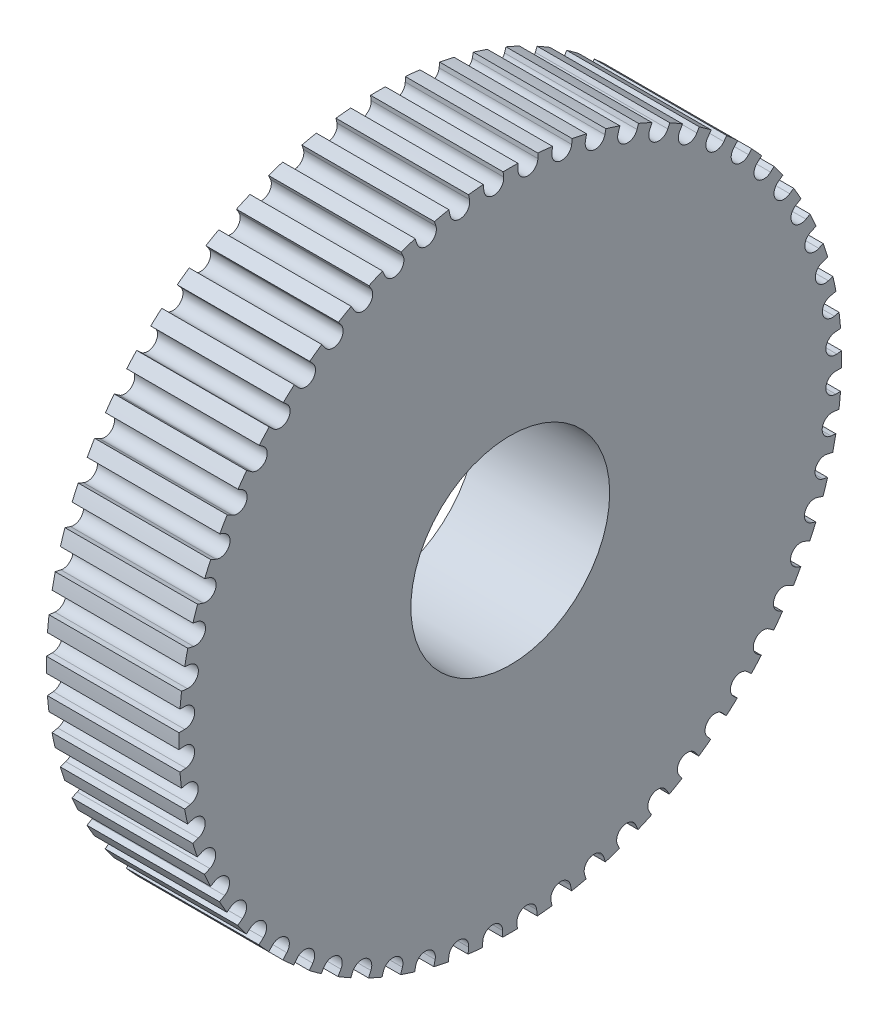
SolidWorks part; units mm, degrees
material "PA Type 6"
ref_plane "Front Plane" through (0, 0, 0) normal (0, 0, 1) x (1, 0, 0)
ref_plane "Top Plane" through (0, 0, 0) normal (0, 1, 0) x (1, 0, 0)
ref_plane "Right Plane" through (0, 0, 0) normal (1, 0, 0) x (0, 0, -1)
sketch "Sketch1" plane through (0, 0, 0) normal (1, 0, 0) x (0, 0, -1)
  circle A0 centre (0, 0) radius 6
  circle A1 centre (0, 0) radius 20
extrude "Boss-Extrude1" add sketch "Sketch1" along normal blind 8
sketch "Sketch2" plane through (8, 0, 0) normal (1, 0, 0) x (0, 0, -1)
  line L0 (1.0615, 20.6675) -> (1.0615, 19.6426) construction
  line L1 (1.6615, 20.6675) -> (1.6615, 19.6426)
  line L2 (0.4615, 20.6675) -> (0.4615, 19.6426)
  arc A0 (1.6615, 20.6675) -> (0.4615, 20.6675) centre (1.0615, 20.6675) ccw
  arc A1 (0.4615, 19.6426) -> (1.6615, 19.6426) centre (1.0615, 19.6426) ccw
  point P2 (1.0615, 20.155)
  point P7 (1.0946, 19.6426)
  point P8 (1.0615, 20.6675)
  dimension "D1" = 0.6
extrude "Cut-Extrude1" cut sketch "Sketch2" against normal blind 10
pattern_circular "CirPattern1" count 60 over 360 about axis through (0, 0, 0) along (1, 0, 0) of "Cut-Extrude1"
